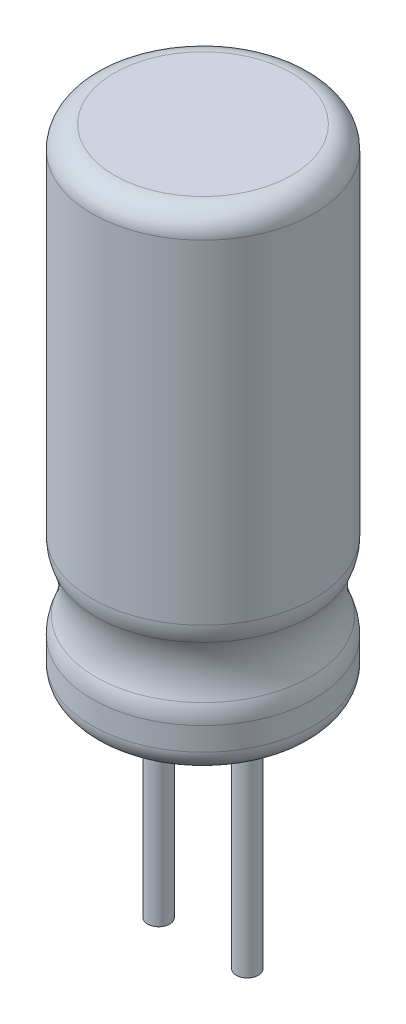
SolidWorks part; units mm, degrees
ref_plane "Front Plane" through (0, 0, 0) normal (0, 0, 1) x (1, 0, 0)
ref_plane "Top Plane" through (0, 0, 0) normal (0, 1, 0) x (1, 0, 0)
ref_plane "Right Plane" through (0, 0, 0) normal (1, 0, 0) x (0, 0, -1)
sketch "Sketch1" plane through (0, 0, 0) normal (0, 1, 0) x (1, 0, 0)
  circle A0 centre (0, 0) radius 2.5
  dimension "D1" = 5
extrude "Boss-Extrude1" add sketch "Sketch1" along normal blind 11
sketch "Sketch2" plane through (0, 0, 0) normal (0, -1, 0) x (1, 0, 0)
  line L0 (-6.4573, 0) -> (7.0651, 0) construction
  circle A0 centre (1, 0) radius 0.25
  circle A1 centre (-1, 0) radius 0.25
  dimension "D3" = 0.5
  dimension "D4" = 0.5
  dimension "D1" = 2
  dimension "D2" = 1
extrude "Boss-Extrude2" add sketch "Sketch2" along normal blind 5
ref_axis "Axis1" through (0, 21.7815, 0) along (0, -1, 0)
sketch "Sketch3" plane through (0, 0, 0) normal (1, 0, 0) x (0, 0, -1)
  line L0 (-9.0697, 2) -> (9.3527, 2) construction
  circle A0 centre (3.8, 2) radius 1.5
  dimension "D3" = 3
  dimension "D1" = 2
  dimension "D2" = 3.8
revolve "Cut-Revolve1" cut sketch "Sketch3" angle 360 about axis through (0, 21.7815, 0) along (0, -1, 0)
fillet "Fillet1" radius 1 2 edges at (0, 1.2517, 2.5) (0, 2.7483, -2.5)
fillet "Fillet2" radius 0.5 1 edges at (0, 11, 2.5)
fillet "Fillet3" radius 0.5 1 edges at (0, 0, 2.5)
